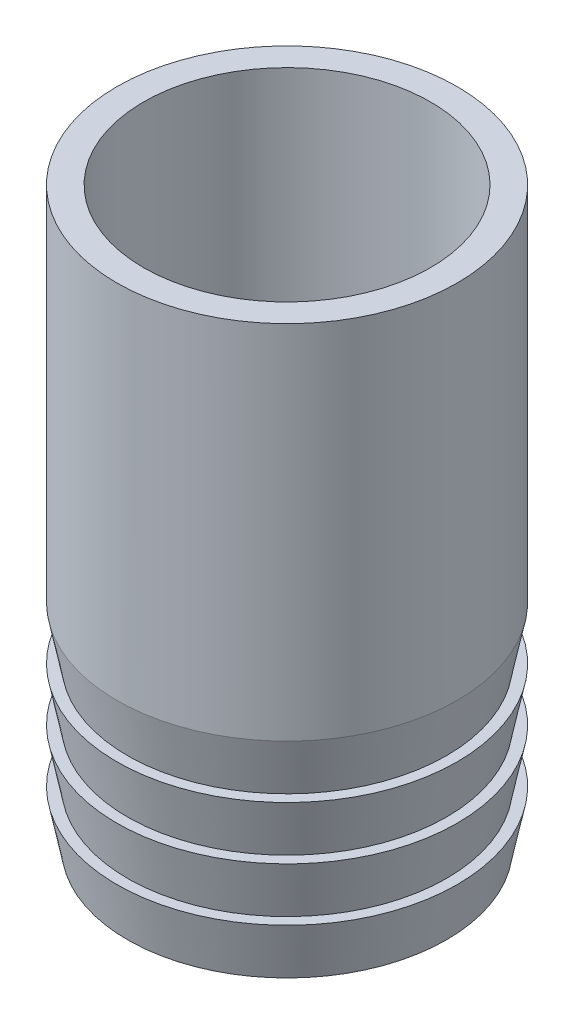
SolidWorks part; units mm, degrees
ref_plane "Front Plane" through (0, 0, 0) normal (0, 0, 1) x (1, 0, 0)
ref_plane "Top Plane" through (0, 0, 0) normal (0, 1, 0) x (1, 0, 0)
ref_plane "Right Plane" through (0, 0, 0) normal (1, 0, 0) x (0, 0, -1)
sketch "Sketch1" plane through (0, 0, 0) normal (0, 1, 0) x (1, 0, 0)
  circle A0 centre (0, 0) radius 16
  circle A1 centre (0, 0) radius 13.5
  dimension "D1" = 27
  dimension "D2" = 32
extrude "Boss-Extrude1" add sketch "Sketch1" along normal blind 54
sketch "Sketch2" plane through (0, 0, 0) normal (0, 0, 1) x (1, 0, 0)
  line L0 (16, 20) -> (15, 15)
  line L1 (16, 0) -> (16, 54) construction
  line L2 (15, 15) -> (16, 15)
  line L3 (16, 15) -> (16, 20)
  line L4 (16, 54) -> (-16, 54) construction
  line L14 (0, 0) -> (0, 54) construction
  line L15 (13.5, 54) -> (-13.5, 54) construction
  line L16 (16, 15) -> (15, 10)
  line L17 (16, 10) -> (16, 15)
  line L18 (15, 10) -> (16, 10)
  line L19 (16, 10) -> (15, 5)
  line L20 (16, 5) -> (16, 10)
  line L21 (15, 5) -> (16, 5)
  line L22 (16, 5) -> (15, 0)
  line L23 (16, 0) -> (16, 5)
  line L24 (15, 0) -> (16, 0)
  dimension "D1" = 5
  dimension "D2" = 1
  dimension "D3" = 34
  dimension "D4" = 4
revolve "Cut-Revolve2" cut sketch "Sketch2" angle 360 about L14
